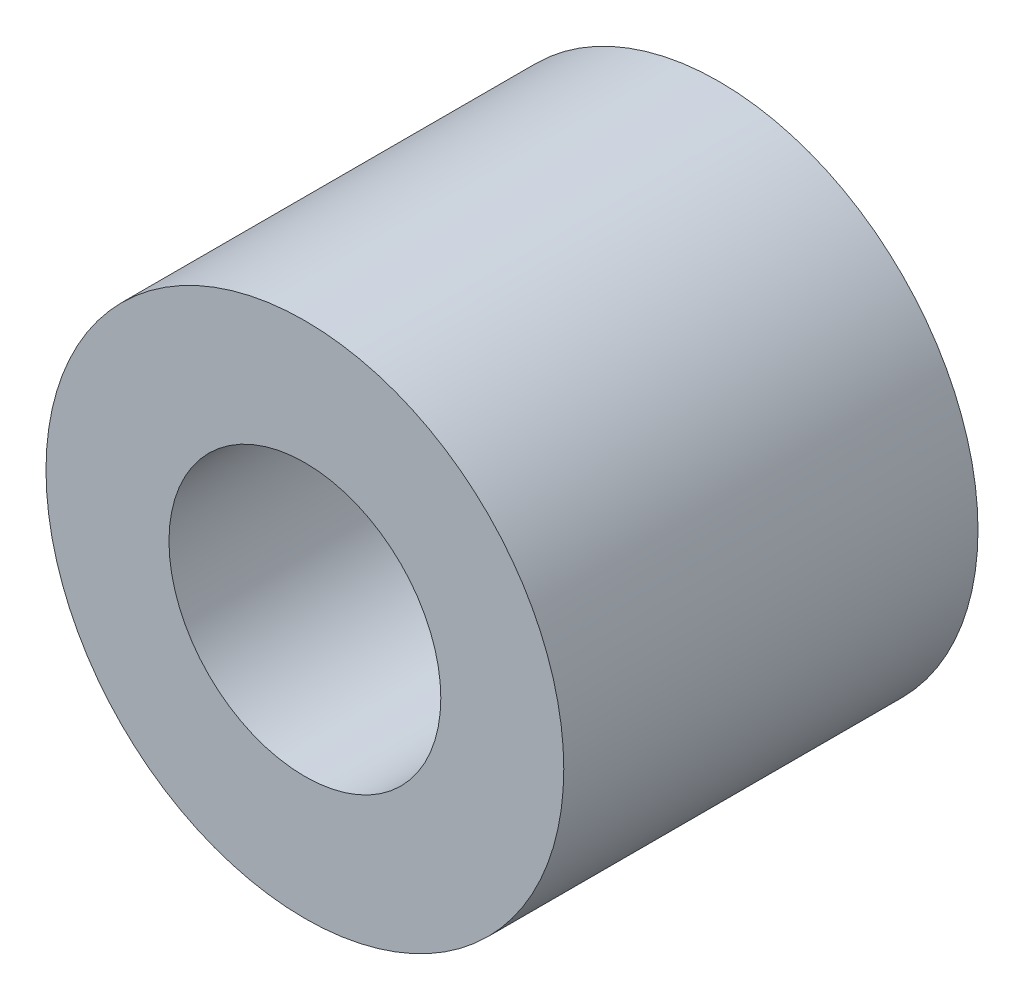
SolidWorks part; units mm, degrees
ref_plane "正面" through (0, 0, 0) normal (0, 0, 1) x (1, 0, 0)
ref_plane "平面" through (0, 0, 0) normal (0, 1, 0) x (1, 0, 0)
ref_plane "右側面" through (0, 0, 0) normal (1, 0, 0) x (0, 0, -1)
sketch "ｽｹｯﾁ1" plane through (0, 0, 0) normal (0, 0, 1) x (1, 0, 0)
  circle A0 centre (0, 0) radius 2.1
  circle A1 centre (0, 0) radius 4
  dimension "D1" = 8
  dimension "D2" = 4.2
extrude "ﾎﾞｽ - 押し出し1" add sketch "ｽｹｯﾁ1" along normal blind 6.4
